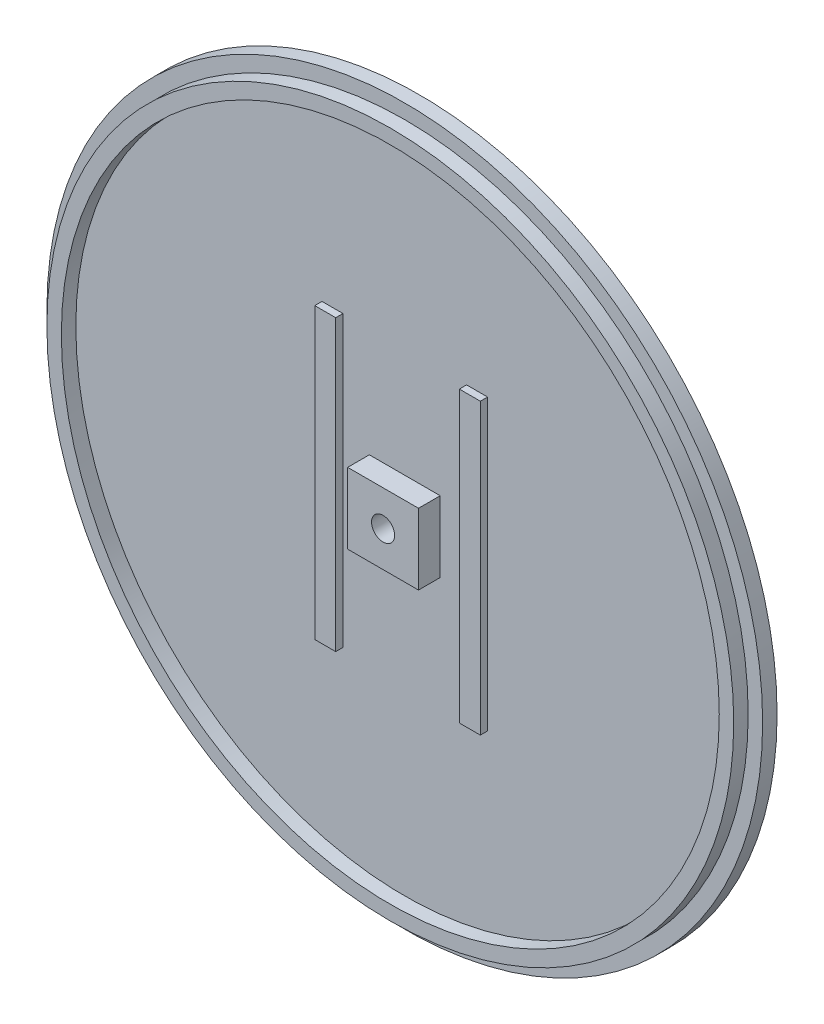
SolidWorks part; units mm, degrees
ref_plane "Front Plane" through (0, 0, 0) normal (0, 0, 1) x (1, 0, 0)
ref_plane "Top Plane" through (0, 0, 0) normal (0, 1, 0) x (1, 0, 0)
ref_plane "Right Plane" through (0, 0, 0) normal (1, 0, 0) x (0, 0, -1)
sketch "Sketch1" plane through (0, 0, 0) normal (0, 0, 1) x (1, 0, 0)
  circle A0 centre (0, 0) radius 49.5
  dimension "D1" = 99
extrude "Main" add sketch "Sketch1" along normal blind 2
sketch "Sketch2" plane through (0, 0, 2) normal (0, 0, 1) x (1, 0, 0)
  line L1 (-11.45, 20) -> (-8.55, 20)
  line L2 (-11.45, 20) -> (-11.45, -20)
  line L3 (-11.45, -20) -> (-8.55, -20)
  line L4 (-8.55, 20) -> (-8.55, -20)
  line L5 (8.5491, 20) -> (11.4509, 20)
  line L6 (8.5491, 20) -> (8.5491, -20)
  line L7 (8.5491, -20) -> (11.4509, -20)
  line L8 (11.4509, 20) -> (11.4509, -20)
  point P8 (-10, 20)
  point P10 (10, 20)
  dimension "D1" = 2.9
  dimension "D2" = 2.9018
  dimension "D3" = 40
  dimension "D4" = 20
  dimension "D5" = 10
  dimension "D6" = 10
extrude "MakerBeamFix" add sketch "Sketch2" along normal blind 1
sketch "Sketch3" plane through (0, 0, 2) normal (0, 0, 1) x (1, 0, 0)
  line L1 (-4.9, 4.9) -> (4.9, 4.9)
  line L2 (-4.9, 4.9) -> (-4.9, -4.9)
  line L3 (-4.9, -4.9) -> (4.9, -4.9)
  line L4 (4.9, 4.9) -> (4.9, -4.9)
  point P4 (0, 4.9)
  point P5 (4.9, 0)
  dimension "D1" = 9.8
  dimension "D2" = 9.8
extrude "CentralFix" add sketch "Sketch3" along normal blind 3
hole_wizard "CSK for M2.5 Flat Head Machine Screw1" positions "Sketch4" profile "Sketch5" countersink size "M2.5" standard "ANSI Metric" end condition through all
sketch "Sketch4" plane through (0, 0, 0) normal (0, 0, -1) x (-1, 0, 0)
  point P0 (0, 0)
sketch "Sketch5" plane through (0, 0, 0) normal (1, 0, 0) x (0, 1, 0)
  line L0 (0, 0) -> (0, 5)
  line L1 (0, 5) -> (1.6, 5)
  line L2 (1.6, 5) -> (1.6, 1.4)
  line L3 (1.6, 1.4) -> (3, 0)
  line L5 (3, 0) -> (0, 0)
  line L6 (-1.6, 1.4) -> (-3, 0) construction
  line L11 (0, -6.35) -> (0, 107.95) construction
  dimension "Thru Hole Dia." = 3.2
  dimension "Thru Hole Depth" = 5
  dimension "Near C'Sink Dia." = 6
  dimension "Near C'Sink Angle" = 90
sketch "Sketch6" plane through (0, 0, 2) normal (0, 0, 1) x (1, 0, 0)
  circle A0 centre (0, 0) radius 47.5
  circle A1 centre (0, 0) radius 45.5
  dimension "D1" = 95
  dimension "D2" = 91
extrude "CircleSupport" add sketch "Sketch6" along normal blind 2
